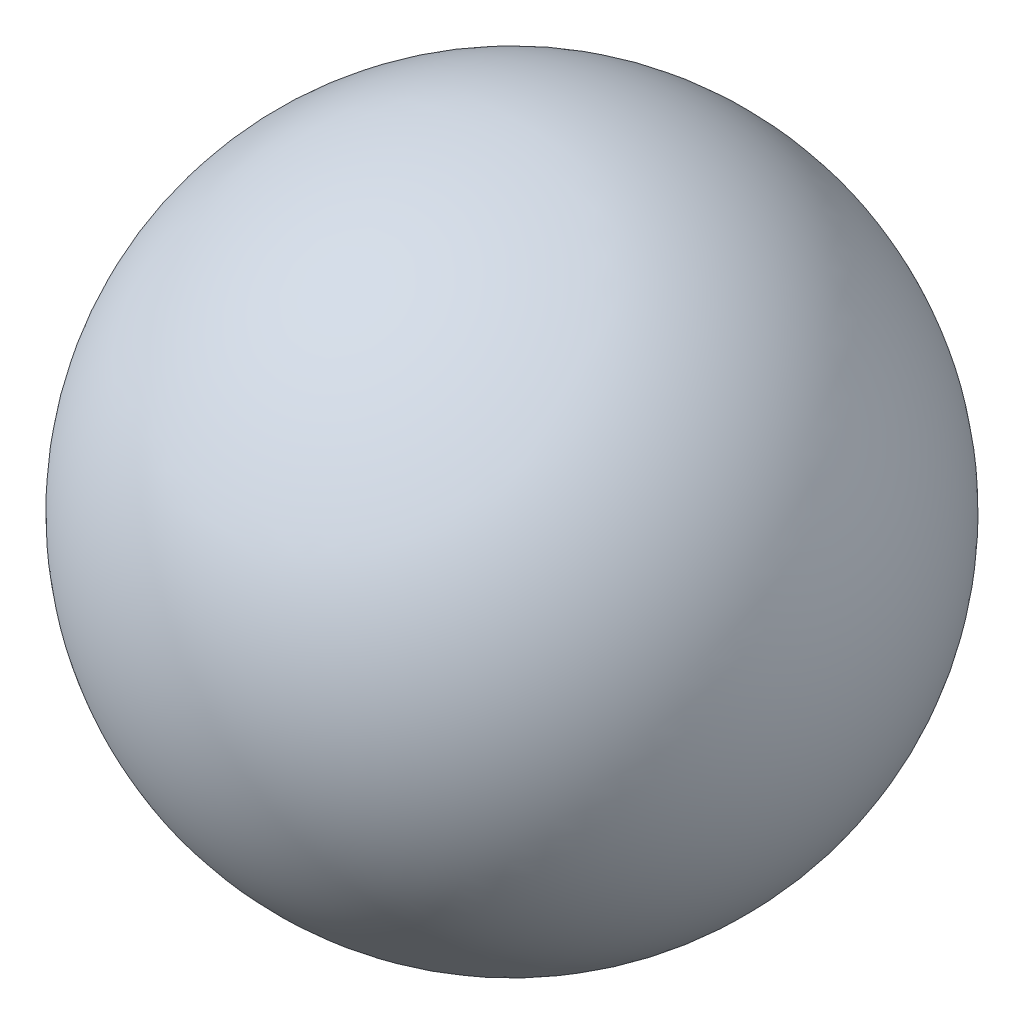
SolidWorks part; units mm, degrees
material "TIMETAL 35A CP Titanium (ASTM Grade 1) 99.1 Ti"
ref_plane "Front Plane" through (0, 0, 0) normal (0, 0, 1) x (1, 0, 0)
ref_plane "Top Plane" through (0, 0, 0) normal (0, 1, 0) x (1, 0, 0)
ref_plane "Right Plane" through (0, 0, 0) normal (1, 0, 0) x (0, 0, -1)
sketch "Sketch1" plane through (0, 0, 0) normal (0, 1, 0) x (1, 0, 0)
  line L0 (0, 164.7) -> (0, -164.7) construction
  line L1 (0, 164.7) -> (0, -164.7)
  arc A1 (0, 164.7) -> (0, -164.7) centre (0, 0) cw
  dimension "D1" = 329.4
  dimension "D2" = 164.7
revolve "Revolve1" add sketch "Sketch1" angle 360 about L0
